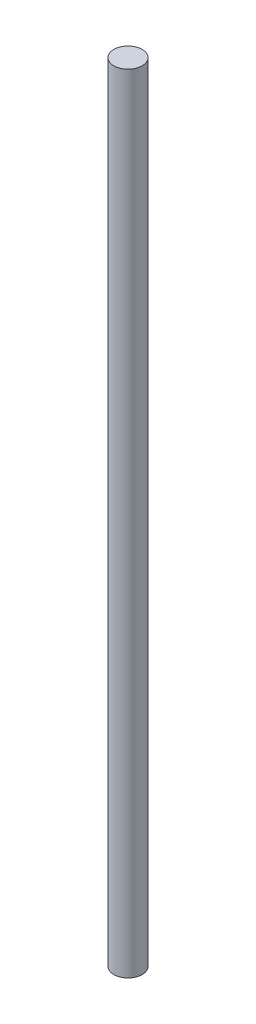
SolidWorks part; units mm, degrees
ref_plane "Front Plane" through (0, 0, 0) normal (0, 0, 1) x (1, 0, 0)
ref_plane "Top Plane" through (0, 0, 0) normal (0, 1, 0) x (1, 0, 0)
ref_plane "Right Plane" through (0, 0, 0) normal (1, 0, 0) x (0, 0, -1)
sketch "Sketch1" plane through (0, 0, 0) normal (0, 0, 1) x (1, 0, 0)
  line L0 (0, 0) -> (0, 264)
  line L1 (0, 0) -> (4.7625, 0)
  line L2 (0, 264) -> (4.7625, 264)
  line L4 (4.7625, 264) -> (4.7625, 0) construction
  line L5 (4.7625, 264) -> (4.7625, 0)
  dimension "D1" = 4.7625
  dimension "D2" = 264
revolve "Revolve1" add sketch "Sketch1" angle 360 about L4
